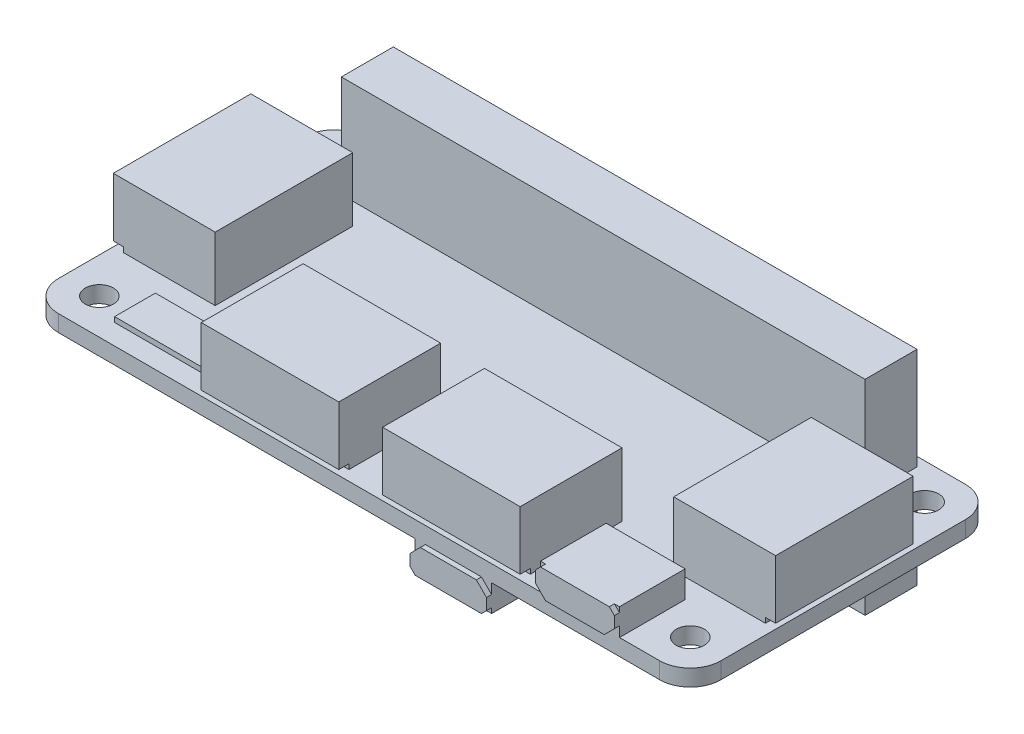
SolidWorks part; units mm, degrees
ref_plane "前视基准面" through (0, 0, 0) normal (0, 0, 1) x (1, 0, 0)
ref_plane "上视基准面" through (0, 0, 0) normal (0, 1, 0) x (1, 0, 0)
ref_plane "右视基准面" through (0, 0, 0) normal (1, 0, 0) x (0, 0, -1)
sketch "草图1" plane through (0, 0, 0) normal (0, 1, 0) x (1, 0, 0)
  line L1 (-29.5, 15) -> (29.5, 15)
  line L2 (-32.5, 12) -> (-32.5, -12)
  line L3 (-29.5, -15) -> (29.5, -15)
  line L4 (32.5, 12) -> (32.5, -12)
  line L5 (-32.5, 15) -> (32.5, -15) construction
  line L6 (-32.5, -15) -> (32.5, 15) construction
  arc A0 (29.5, 15) -> (32.5, 12) centre (29.5, 12) cw
  arc A1 (29.5, -15) -> (32.5, -12) centre (29.5, -12) ccw
  arc A2 (-32.5, -12) -> (-29.5, -15) centre (-29.5, -12) ccw
  arc A3 (-29.5, 15) -> (-32.5, 12) centre (-29.5, 12) ccw
  point P0 (0, 0)
  dimension "D3" = 3
  dimension "D1" = 65
  dimension "D2" = 30
extrude "凸台-拉伸1" add sketch "草图1" along normal blind 1.62
sketch "草图2" plane through (0, 1.62, 0) normal (0, 1, 0) x (1, 0, 0)
  line L0 (-29.5, -15) -> (29.5, -15) construction
  line L1 (32.5, -12) -> (32.5, 12) construction
  line L2 (29.5, 15) -> (-29.5, 15) construction
  circle A0 centre (29, -11.5) radius 1.375
  circle A1 centre (29, 11.5) radius 1.375
  circle A2 centre (-29, -11.5) radius 1.375
  circle A3 centre (-29, 11.5) radius 1.375
  dimension "D1" = 2.75
  dimension "D2" = 3.5
  dimension "D3" = 3.5
  dimension "D4" = 3.5
  dimension "D5" = 3.5
extrude "切除-拉伸1" cut sketch "草图2" against normal up to next
sketch "草图11" plane through (0, 0, 0) normal (0, -1, 0) x (1, 0, 0)
  line L0 (29.5, -15) -> (-29.5, -15) construction
  line L1 (25.65, -14.1) -> (-25.75, -14.1)
  line L2 (25.65, -14.1) -> (25.65, -9)
  line L3 (25.65, -9) -> (-25.75, -9)
  line L4 (-25.75, -14.1) -> (-25.75, -9)
  line L5 (32.5, 12) -> (32.5, -12) construction
  dimension "D1" = 51.4
  dimension "D2" = 5.1
  dimension "D3" = 0.9
  dimension "D4" = 6.85
extrude "凸台-拉伸9" add sketch "草图11" along normal blind 8.45
sketch "草图12" plane through (0, 1.62, 0) normal (0, 1, 0) x (1, 0, 0)
  line L4 (25.65, 9) -> (25.65, 14.1)
  line L5 (-25.75, 9) -> (25.65, 9)
  line L6 (-25.75, 14.1) -> (-25.75, 9)
  line L7 (25.65, 14.1) -> (-25.75, 14.1)
  line L8 (25.65, 9) -> (25.65, 14.1)
  line L9 (-25.75, 9) -> (25.65, 9)
  line L10 (-25.75, 14.1) -> (-25.75, 9)
  line L11 (25.65, 14.1) -> (-25.75, 14.1)
  dimension "D1" = 0
extrude "凸台-拉伸10" add sketch "草图12" along normal blind 10
sketch "草图13" plane through (0, 1.62, 0) normal (0, 1, 0) x (1, 0, 0)
  line L0 (-32.5, 12) -> (-32.5, -12) construction
  line L1 (-32.5, 6.87) -> (-22.5, 6.87)
  line L2 (-32.5, 6.87) -> (-32.5, -6.63)
  line L3 (-32.5, -6.63) -> (-22.5, -6.63)
  line L4 (-22.5, 6.87) -> (-22.5, -6.63)
  line L5 (32.5, -12) -> (32.5, 12) construction
  line L6 (32.5, 6.87) -> (22.5, 6.87)
  line L7 (32.5, 6.87) -> (32.5, -6.63)
  line L8 (32.5, -6.63) -> (22.5, -6.63)
  line L9 (22.5, 6.87) -> (22.5, -6.63)
  line L10 (-29.5, -15) -> (29.5, -15) construction
  line L11 (-15.5, -15) -> (-2, -15)
  line L12 (-15.5, -15) -> (-15.5, -5)
  line L13 (-15.5, -5) -> (-2, -5)
  line L14 (-2, -15) -> (-2, -5)
  line L15 (29.5, 15) -> (-29.5, 15) construction
  line L16 (2.3, -15) -> (15.8, -15)
  line L17 (2.3, -15) -> (2.3, -5)
  line L18 (2.3, -5) -> (15.8, -5)
  line L19 (15.8, -15) -> (15.8, -5)
  dimension "D1" = 13.5
  dimension "D2" = 10
  dimension "D3" = 4.3
  dimension "D4" = 17
  dimension "D8" = 8.13
extrude "凸台-拉伸12" add sketch "草图13" along normal blind 6.25
sketch "草图14" plane through (0, 0, 15) normal (0, 0, 1) x (1, 0, 0)
  line L0 (-2, 7.87) -> (-2, 1.62) construction
  line L1 (-15.5, 1.62) -> (-2, 1.62)
  line L2 (-15.5, 1.62) -> (-15.5, 2.12)
  line L3 (-15.5, 2.12) -> (-2, 2.12)
  line L4 (-2, 1.62) -> (-2, 2.12)
  line L5 (15.8, 7.87) -> (15.8, 1.62) construction
  line L6 (2.3, 1.62) -> (15.8, 1.62)
  line L7 (2.3, 1.62) -> (2.3, 2.12)
  line L8 (2.3, 2.12) -> (15.8, 2.12)
  line L9 (15.8, 1.62) -> (15.8, 2.12)
  dimension "D1" = 0.5
  dimension "D2" = 0.5
extrude "切除-拉伸2" cut sketch "草图14" against normal blind 1
sketch "草图15" plane through (-32.5, 0, 0) normal (-1, 0, 0) x (0, 0, 1)
  line L0 (6.63, 7.87) -> (6.63, 1.62) construction
  line L1 (-6.87, 1.62) -> (6.63, 1.62)
  line L2 (-6.87, 1.62) -> (-6.87, 2.12)
  line L3 (-6.87, 2.12) -> (6.63, 2.12)
  line L4 (6.63, 1.62) -> (6.63, 2.12)
  dimension "D1" = 0.5
extrude "切除-拉伸3" cut sketch "草图15" against normal blind 1
sketch "草图16" plane through (32.5, 0, 0) normal (1, 0, 0) x (0, 0, -1)
  line L0 (6.87, 7.87) -> (6.87, 1.62) construction
  line L1 (-6.63, 1.62) -> (6.87, 1.62)
  line L2 (-6.63, 1.62) -> (-6.63, 2.12)
  line L3 (-6.63, 2.12) -> (6.87, 2.12)
  line L4 (6.87, 1.62) -> (6.87, 2.12)
  dimension "D1" = 0.5
extrude "切除-拉伸4" cut sketch "草图16" against normal blind 1
sketch "草图17" plane through (0, 1.62, 0) normal (0, 1, 0) x (1, 0, 0)
  line L0 (-29.5, -15) -> (29.5, -15) construction
  line L1 (17.8, -15) -> (25.55, -15)
  line L2 (17.8, -15) -> (17.8, -8.56)
  line L3 (17.8, -8.56) -> (25.55, -8.56)
  line L4 (25.55, -15) -> (25.55, -8.56)
  dimension "D1" = 6.44
  dimension "D2" = 7.75
  dimension "D3" = 2
extrude "凸台-拉伸13" add sketch "草图17" along normal blind 2.62
sketch "草图18" plane through (0, 0, 15) normal (0, 0, 1) x (1, 0, 0)
  line L0 (17.8, 2.62) -> (18.8, 1.62)
  line L1 (18.3, 4.24) -> (25.05, 4.24)
  line L2 (17.8, 3.74) -> (17.8, 2.62)
  line L3 (18.8, 1.62) -> (24.55, 1.62)
  line L4 (25.55, 3.74) -> (25.55, 2.62)
  line L5 (24.55, 1.62) -> (25.55, 2.62)
  line L6 (17.8, 3.74) -> (18.3, 4.24)
  line L7 (25.05, 4.24) -> (25.55, 3.74)
  point P0 (17.8, 4.24)
  point P1 (25.55, 1.62)
  point P2 (17.8, 1.62)
  point P3 (25.55, 4.24)
extrude "凸台-拉伸14" add sketch "草图18" along normal blind 0.5
sketch "草图19" plane through (0, 1.62, 0) normal (0, 1, 0) x (1, 0, 0)
  line L0 (-15.5, -5) -> (-15.5, -14) construction
  line L1 (-26, -9) -> (-17.5, -9)
  line L2 (-26, -9) -> (-26, -13)
  line L3 (-26, -13) -> (-17.5, -13)
  line L4 (-17.5, -9) -> (-17.5, -13)
  line L5 (-29.5, -15) -> (17.8, -15) construction
  dimension "D1" = 8.5
  dimension "D2" = 2
  dimension "D3" = 2
  dimension "D4" = 4
extrude "凸台-拉伸15" add sketch "草图19" along normal blind 0.5
sketch "草图20" plane through (0, 0, 0) normal (0, -1, 0) x (1, 0, 0)
  line L0 (-29.5, 15) -> (29.5, 15) construction
  line L1 (5.5, 15) -> (13, 15)
  line L2 (5.5, 15) -> (5.5, 9.8536)
  line L3 (5.5, 9.8536) -> (13, 9.8536)
  line L4 (13, 15) -> (13, 9.8536)
  line L5 (32.5, 12) -> (32.5, -12) construction
  dimension "D1" = 19.5
  dimension "D2" = 7.5
extrude "凸台-拉伸16" add sketch "草图20" along normal blind 2.62
sketch "草图21" plane through (0, 0, 15) normal (0, 0, 1) x (1, 0, 0)
  line L0 (13, -2.62) -> (13, 0) construction
  line L1 (6.5, 0) -> (12, 0)
  line L2 (5.5, -1) -> (5.5, -2.12)
  line L3 (6, -2.62) -> (12.5, -2.62)
  line L4 (13, -1) -> (13, -2.12)
  line L5 (12.5, -2.62) -> (13, -2.12)
  line L6 (5.5, -2.12) -> (6, -2.62)
  line L7 (5.5, -1) -> (6.5, 0)
  line L8 (12, 0) -> (13, -1)
  point P0 (5.5, 0)
  point P1 (13, -2.62)
  point P2 (5.5, -2.62)
  point P3 (13, 0)
extrude "凸台-拉伸17" add sketch "草图21" along normal blind 0.5
